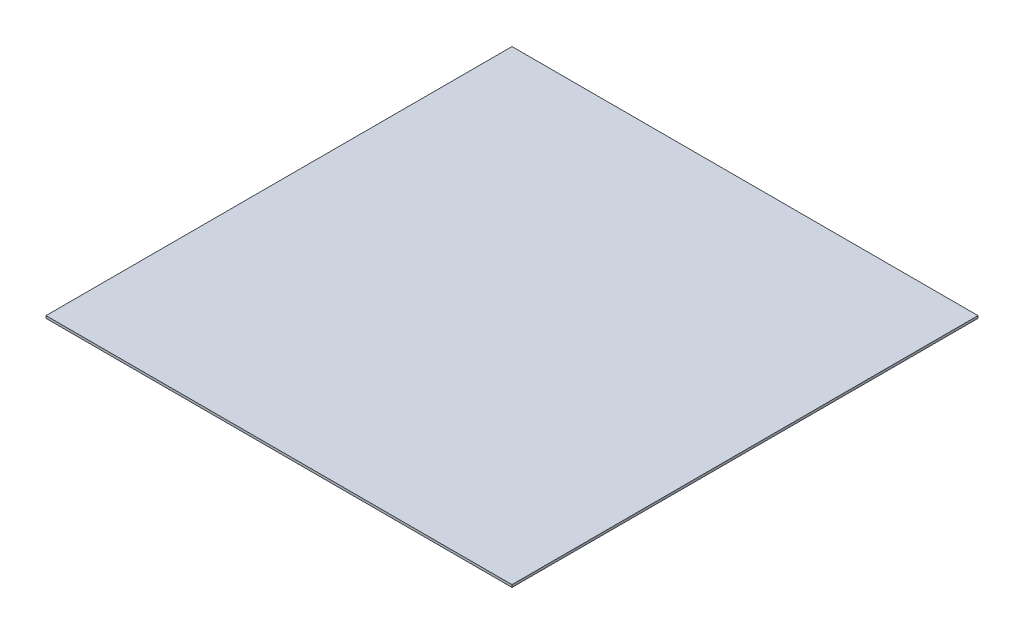
SolidWorks part; units mm, degrees
ref_plane "Front Plane" through (0, 0, 0) normal (0, 0, 1) x (1, 0, 0)
ref_plane "Top Plane" through (0, 0, 0) normal (0, 1, 0) x (1, 0, 0)
ref_plane "Right Plane" through (0, 0, 0) normal (1, 0, 0) x (0, 0, -1)
sketch "Sketch1" plane through (0, 0, 0) normal (0, 1, 0) x (1, 0, 0)
  line L1 (-303.276, -303.276) -> (303.276, -303.276)
  line L2 (-303.276, -303.276) -> (-303.276, 303.276)
  line L3 (-303.276, 303.276) -> (303.276, 303.276)
  line L4 (303.276, -303.276) -> (303.276, 303.276)
  line L5 (-303.276, -303.276) -> (303.276, 303.276) construction
  line L6 (-303.276, 303.276) -> (303.276, -303.276) construction
  point P0 (0, 0)
  dimension "D1" = 606.552
extrude "Boss-Extrude1" add sketch "Sketch1" along normal blind 3.175
sketch "Sketch3" plane through (0, 3.175, 0) normal (0, 1, 0) x (1, 0, 0)
  line L0 (0, -200) -> (0, 200)
  line L1 (-200, -50) -> (200, -50)
  line L2 (-200, 0) -> (200, 0)
  line L3 (-200, -100) -> (200, -100)
  line L4 (-50, -200) -> (-50, 200)
  line L5 (-100, -200) -> (-100, 200)
  line L6 (-150, -200) -> (-150, 200)
  line L7 (-200, -200) -> (-200, 200)
  line L8 (0, -200) -> (0, 200)
  line L9 (-50, -200) -> (-50, 200)
  line L10 (-100, -200) -> (-100, 200)
  line L11 (-150, -200) -> (-150, 200)
  line L12 (50, -200) -> (50, 200)
  line L13 (0, -200) -> (0, 200)
  line L14 (-50, -200) -> (-50, 200)
  line L15 (-100, -200) -> (-100, 200)
  line L16 (100, -200) -> (100, 200)
  line L17 (50, -200) -> (50, 200)
  line L18 (0, -200) -> (0, 200)
  line L19 (-50, -200) -> (-50, 200)
  line L20 (150, -200) -> (150, 200)
  line L21 (100, -200) -> (100, 200)
  line L22 (50, -200) -> (50, 200)
  line L23 (0, -200) -> (0, 200)
  line L24 (50, -200) -> (50, 200)
  line L25 (100, -200) -> (100, 200)
  line L26 (150, -200) -> (150, 200)
  line L27 (200, -200) -> (200, 200)
  line L28 (-200, -150) -> (200, -150)
  line L29 (-200, -200) -> (200, -200)
  line L30 (-200, 0) -> (200, 0)
  line L31 (-200, -50) -> (200, -50)
  line L32 (-200, -100) -> (200, -100)
  line L33 (-200, -150) -> (200, -150)
  line L34 (-200, 50) -> (200, 50)
  line L35 (-200, 0) -> (200, 0)
  line L36 (-200, -50) -> (200, -50)
  line L37 (-200, -100) -> (200, -100)
  line L38 (-200, 100) -> (200, 100)
  line L39 (-200, 50) -> (200, 50)
  line L40 (-200, 0) -> (200, 0)
  line L41 (-200, -50) -> (200, -50)
  line L42 (-200, 150) -> (200, 150)
  line L43 (-200, 100) -> (200, 100)
  line L44 (-200, 50) -> (200, 50)
  line L45 (-200, 0) -> (200, 0)
  line L46 (-200, 50) -> (200, 50)
  line L47 (-200, 100) -> (200, 100)
  line L48 (-200, 150) -> (200, 150)
  line L49 (-200, 200) -> (200, 200)
  point P6 (0, 0)
  point P12 (0, 0)
  dimension "D3" = 400
  dimension "D4" = 400
  dimension "D1" = 5
  dimension "D2" = 5
  dimension "D5" = 5
  dimension "D6" = 5
